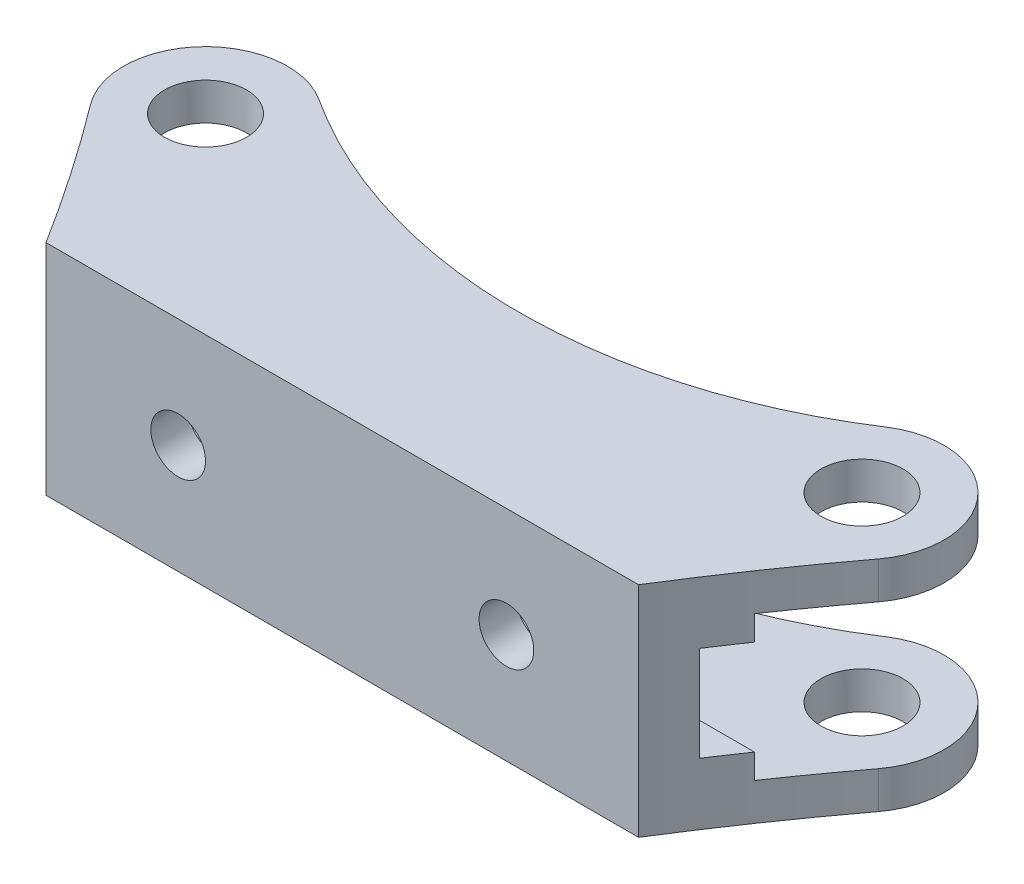
SolidWorks part; units mm, degrees
material "6061-T6 (SS)"
ref_plane "Front Plane" through (0, 0, 0) normal (0, 0, 1) x (1, 0, 0)
ref_plane "Top Plane" through (0, 0, 0) normal (0, 1, 0) x (1, 0, 0)
ref_plane "Right Plane" through (0, 0, 0) normal (1, 0, 0) x (0, 0, -1)
sketch "Sketch1" plane through (0, 0, 0) normal (1, 0, 0) x (0, 0, -1)
  line L0 (0, 0) -> (19.05, 0) construction
  line L1 (19.05, 8.382) -> (19.05, -8.382) construction
  dimension "D1" = 19.05
  dimension "D2" = 16.764
sketch "Sketch2" plane through (0, 0, 0) normal (1, 0, 0) x (0, 0, -1)
  line L0 (0, 0) -> (4.318, 0) construction
  line L1 (4.318, -8.382) -> (4.318, 8.382)
  line L2 (4.318, 8.382) -> (31.75, 8.382)
  line L3 (31.75, 8.382) -> (31.75, 12.7)
  line L4 (31.75, 12.7) -> (0, 12.7)
  line L5 (0, 12.7) -> (0, -12.7)
  line L7 (4.318, -8.382) -> (31.75, -8.382)
  line L8 (31.75, -8.382) -> (31.75, -12.7)
  line L9 (31.75, -12.7) -> (0, -12.7)
  line L10 (22.225, 12.7) -> (22.225, 8.382) construction
  line L11 (22.225, 8.382) -> (22.225, -8.382) construction
  line L12 (22.225, -8.382) -> (22.225, -12.7) construction
  dimension "D1" = 25.4
  dimension "D2" = 31.75
  dimension "D3" = 22.225
extrude "Extrude1" add sketch "Sketch2" along normal mid plane 95.25
sketch "Sketch4" plane through (0, 0, 0) normal (0, 1, 0) x (1, 0, 0)
  line L0 (0, 31.75) -> (0, 0) construction
  line L1 (47.625, 31.75) -> (-47.625, 31.75) construction
  line L2 (47.625, 0) -> (-47.625, 0) construction
  circle A0 centre (38.1, 22.225) radius 4.7625
  circle A1 centre (-38.1, 22.225) radius 4.7625
  dimension "D1" = 9.525
  dimension "D2" = 38.1
  dimension "D3" = 22.225
extrude "SphericalHoles" cut sketch "Sketch4" against normal through all and the other way through all
fillet "Fillet1" radius 9.525 4 edges at (47.625, -10.541, -31.75) (-47.625, -10.541, -31.75) (-47.625, 10.541, -31.75) (47.625, 10.541, -31.75)
sketch "Sketch5" plane through (0, 0, -4.318) normal (0, 0, -1) x (-1, 0, 0)
  line L0 (0, 8.382) -> (0, -8.382) construction
  line L1 (-47.625, 8.382) -> (47.625, 8.382) construction
  line L2 (0, 8.382) -> (0, -8.382) construction
  line L3 (-47.625, -8.382) -> (47.625, -8.382) construction
  circle A0 centre (19.05, 0) radius 3.175
  circle A1 centre (-19.05, 0) radius 3.175
  dimension "D2" = 6.35
  dimension "D1" = 38.1
extrude "Extrude2" cut sketch "Sketch5" against normal through all
sketch "Sketch6" plane through (0, 0, 0) normal (1, 0, 0) x (0, 0, -1)
  line L0 (0, 0) -> (19.05, 0) construction
  line L1 (0, 12.7) -> (0, -12.7) construction
  line L2 (8.128, -8.382) -> (8.128, -5.5245)
  line L3 (4.318, 8.382) -> (8.128, 8.382)
  line L4 (4.318, 8.382) -> (4.318, 5.5245)
  line L5 (4.318, 5.5245) -> (8.128, 5.5245)
  line L6 (8.128, 8.382) -> (8.128, 5.5245)
  line L7 (4.318, -5.5245) -> (8.128, -5.5245)
  line L8 (4.318, -8.382) -> (4.318, -5.5245)
  line L9 (4.318, -8.382) -> (8.128, -8.382)
  dimension "D1" = 11.049
  dimension "D2" = 3.81
extrude "Extrude3" add sketch "Sketch6" along normal up to surface and the other way up to surface
sketch3d "3DSketch1"
  line L0 (38.1, 12.7, -22.225) -> (38.1, -12.7, -22.225) construction
  line L1 (38.1, 8.382, -22.225) -> (38.1, 12.7, -22.225) construction
  line L2 (38.1, -12.7, -22.225) -> (38.1, -8.382, -22.225) construction
  line L3 (-38.1, 12.7, -22.225) -> (-38.1, -12.7, -22.225) construction
  line L4 (-38.1, 8.382, -22.225) -> (-38.1, 12.7, -22.225) construction
  line L5 (-38.1, -12.7, -22.225) -> (-38.1, -8.382, -22.225) construction
  point P6 (38.1, 0, -22.225)
  point P13 (-38.1, 0, -22.225)
  point P14 (0, 0, 0)
sketch "Sketch10" plane through (0, 0, 0) normal (0, 0, 1) x (1, 0, 0)
  line L0 (-34.3916, 12.7) -> (-34.3916, -12.7) construction
  line L1 (47.625, 12.7) -> (-47.625, 12.7) construction
  line L2 (47.625, -12.7) -> (-47.625, -12.7) construction
  line L3 (0, 12.7) -> (0, -12.7) construction
  line L4 (34.3916, 12.7) -> (34.3916, -12.7) construction
  dimension "D1" = 68.7832
sketch "Sketch12" plane through (0, 12.7, 0) normal (0, 1, 0) x (1, 0, 0)
  line L0 (47.625, 0) -> (-47.625, 0) construction
  line L1 (-47.625, 22.225) -> (-47.625, 0) construction
  line L2 (-34.3916, 0) -> (-47.625, 0)
  line L3 (-47.625, 22.225) -> (-47.625, 0)
  line L4 (0, 0) -> (0, 31.75) construction
  line L5 (38.1, 31.75) -> (-38.1, 31.75) construction
  line L6 (47.625, 22.225) -> (47.625, 0)
  line L7 (34.3916, 0) -> (47.625, 0)
  arc A0 (-47.625, 22.225) -> (-45.72, 16.51) centre (-38.1, 22.225) ccw
  arc A1 (-34.3916, 0) -> (-45.72, 16.51) centre (-235.8883, -126.1162) ccw
  arc A2 (34.3916, 0) -> (45.72, 16.51) centre (235.8883, -126.1162) cw
  arc A3 (47.625, 22.225) -> (45.72, 16.51) centre (38.1, 22.225) cw
  point P6 (-34.3916, 0)
  dimension "D1" = 1.905
extrude "Cut-Extrude1" cut sketch "Sketch12" against normal through all
sketch "Sketch13" plane through (0, 12.7, 0) normal (0, 1, 0) x (1, 0, 0)
  line L0 (45.72, 16.51) -> (30.48, 27.94) construction
  line L1 (38.1, 31.75) -> (-38.1, 31.75)
  arc A0 (45.72, 16.51) -> (38.1, 31.75) centre (38.1, 22.225) ccw construction
  arc A1 (38.1, 31.75) -> (32.9045, 30.2083) centre (38.1, 22.225) ccw
  arc A2 (-38.1, 31.75) -> (-45.72, 16.51) centre (-38.1, 22.225) ccw construction
  arc A3 (-32.9045, 30.2083) -> (-38.1, 31.75) centre (-38.1, 22.225) ccw
  arc A4 (-32.9045, 30.2083) -> (32.9045, 30.2083) centre (0, 80.7691) ccw
  dimension "D1" = 120.65
extrude "Cut-Extrude3" cut sketch "Sketch13" against normal through all
